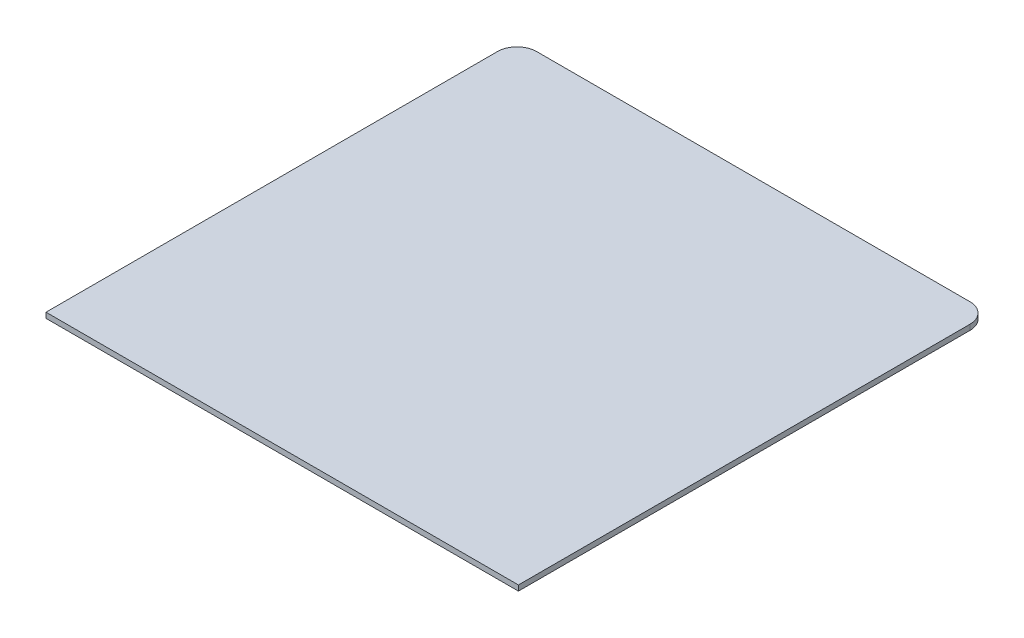
SolidWorks part; units mm, degrees
ref_plane "Front Plane" through (0, 0, 0) normal (0, 0, 1) x (1, 0, 0)
ref_plane "Top Plane" through (0, 0, 0) normal (0, 1, 0) x (1, 0, 0)
ref_plane "Right Plane" through (0, 0, 0) normal (1, 0, 0) x (0, 0, -1)
sketch "Sketch1" plane through (0, 0, 0) normal (0, 1, 0) x (1, 0, 0)
  line L0 (0, 0) -> (9680, 0)
  line L1 (0, 0) -> (0, 9252)
  line L3 (9680, 0) -> (9680, 9252)
  line L4 (9280, 9652) -> (400, 9652)
  arc A0 (0, 9252) -> (400, 9652) centre (400, 9252) cw
  arc A1 (9680, 9252) -> (9280, 9652) centre (9280, 9252) ccw
  dimension "D1" = 9680
  dimension "D2" = 9252
extrude "Boss-Extrude1" add sketch "Sketch1" along normal blind 110
